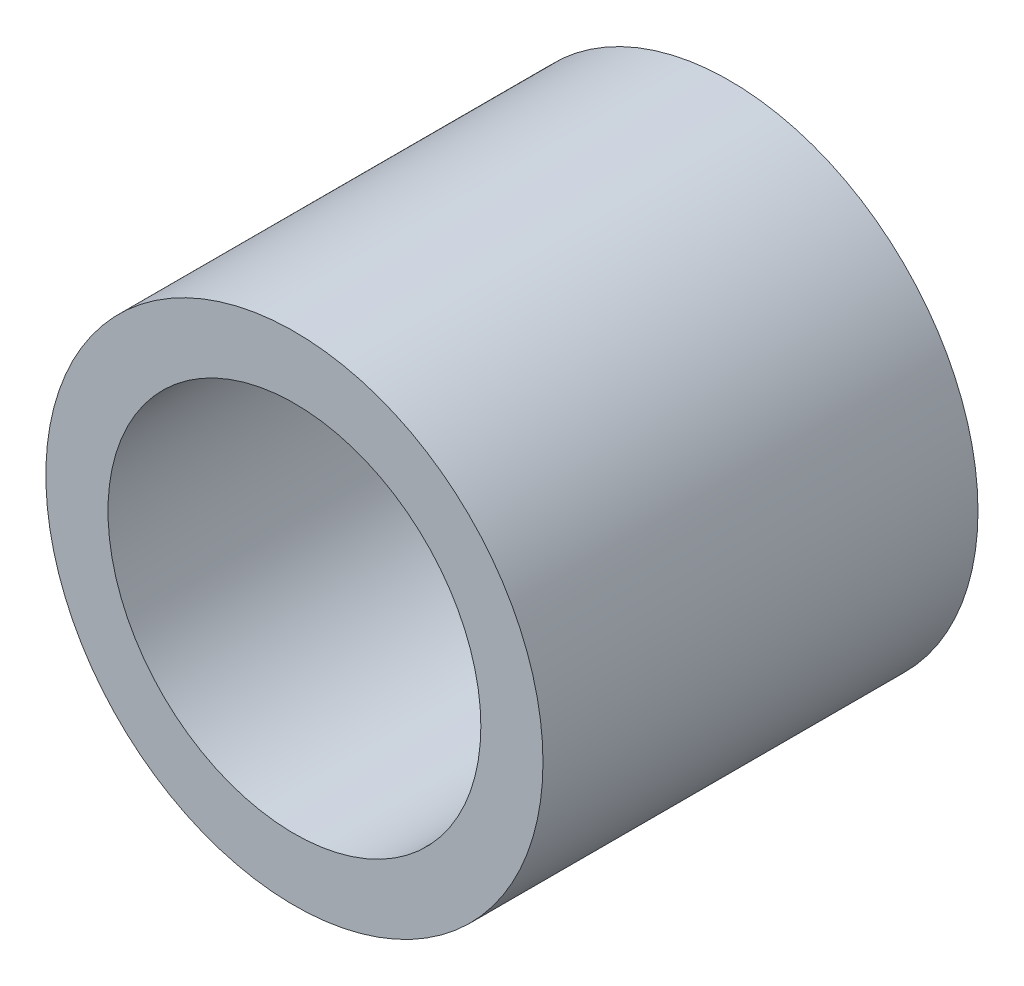
SolidWorks part; units mm, degrees
ref_plane "Front Plane" through (0, 0, 0) normal (0, 0, 1) x (1, 0, 0)
ref_plane "Top Plane" through (0, 0, 0) normal (0, 1, 0) x (1, 0, 0)
ref_plane "Right Plane" through (0, 0, 0) normal (1, 0, 0) x (0, 0, -1)
sketch "Sketch1" plane through (0, 0, 0) normal (0, 0, 1) x (1, 0, 0)
  circle A1 centre (0, 0) radius 4
  circle A2 centre (0, 0) radius 1.9
extrude "Boss-Extrude1" add sketch "Sketch1" along normal blind 7
sketch "Sketch2" plane through (0, 0, 7) normal (0, 0, 1) x (1, 0, 0)
  circle A0 centre (0, 0) radius 3
extrude "Cut-Extrude1" cut sketch "Sketch2" against normal blind 5
